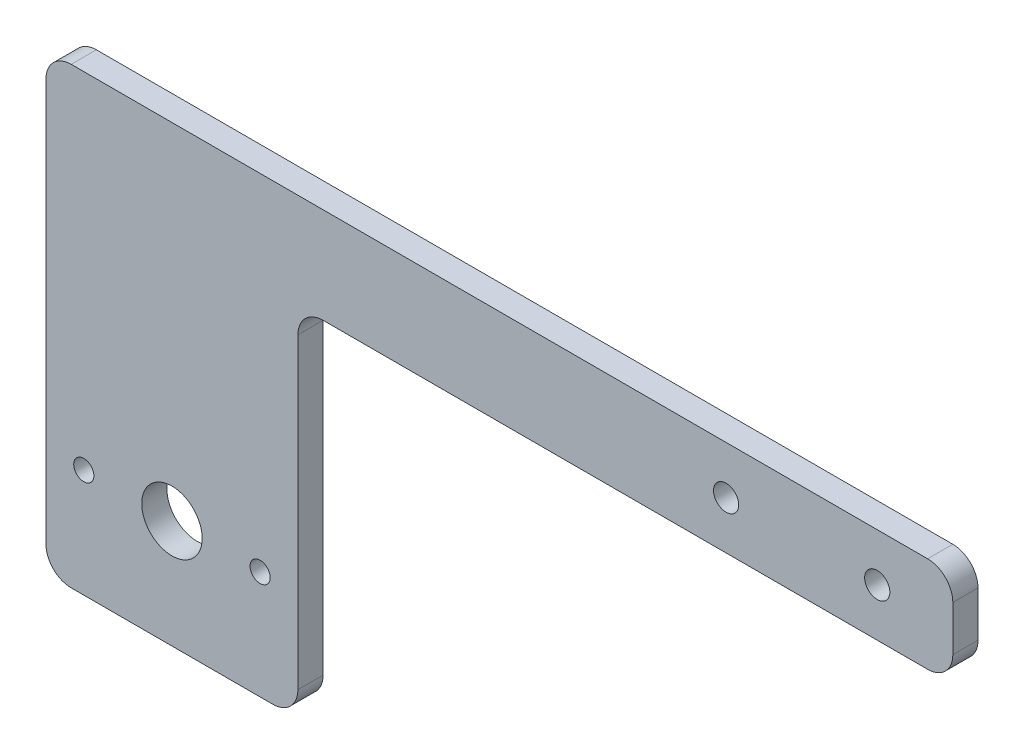
SolidWorks part; units mm, degrees
material "6061 Alloy"
ref_plane "Front Plane" through (0, 0, 0) normal (0, 0, 1) x (1, 0, 0)
ref_plane "Top Plane" through (0, 0, 0) normal (0, 1, 0) x (1, 0, 0)
ref_plane "Right Plane" through (0, 0, 0) normal (1, 0, 0) x (0, 0, -1)
sketch "Sketch1" plane through (0, 0, 0) normal (0, 0, 1) x (1, 0, 0)
  line L0 (0, 0) -> (180, 0)
  line L1 (180, 0) -> (180, -19)
  line L2 (180, -19) -> (50, -19)
  line L3 (50, -19) -> (50, -90)
  line L4 (50, -90) -> (0, -90)
  line L5 (0, -90) -> (0, 0)
  circle A0 centre (135, -9.5) radius 2.5
  circle A1 centre (165, -9.5) radius 2.5
  circle A2 centre (25, -68.5) radius 6
  circle A3 centre (7.5, -68.5) radius 2
  circle A4 centre (42.5, -68.5) radius 2
  dimension "D2" = 15
  dimension "D3" = 5
  dimension "D5" = 9.5
  dimension "D6" = 30
  dimension "D9" = 12
  dimension "D10" = 25
  dimension "D11" = 49.5
  dimension "D12" = 4
  dimension "D13" = 35
  dimension "D14" = 7.5
  dimension "D1" = 180
  dimension "D4" = 19
  dimension "D7" = 50
  dimension "D8" = 90
extrude "Boss-Extrude1" add sketch "Sketch1" along normal blind 5
fillet "Fillet1" radius 5 6 edges at (0, 0, 2.5) (0, -90, 2.5) (50, -90, 2.5) (50, -19, 2.5) (180, -19, 2.5) (180, 0, 2.5)
